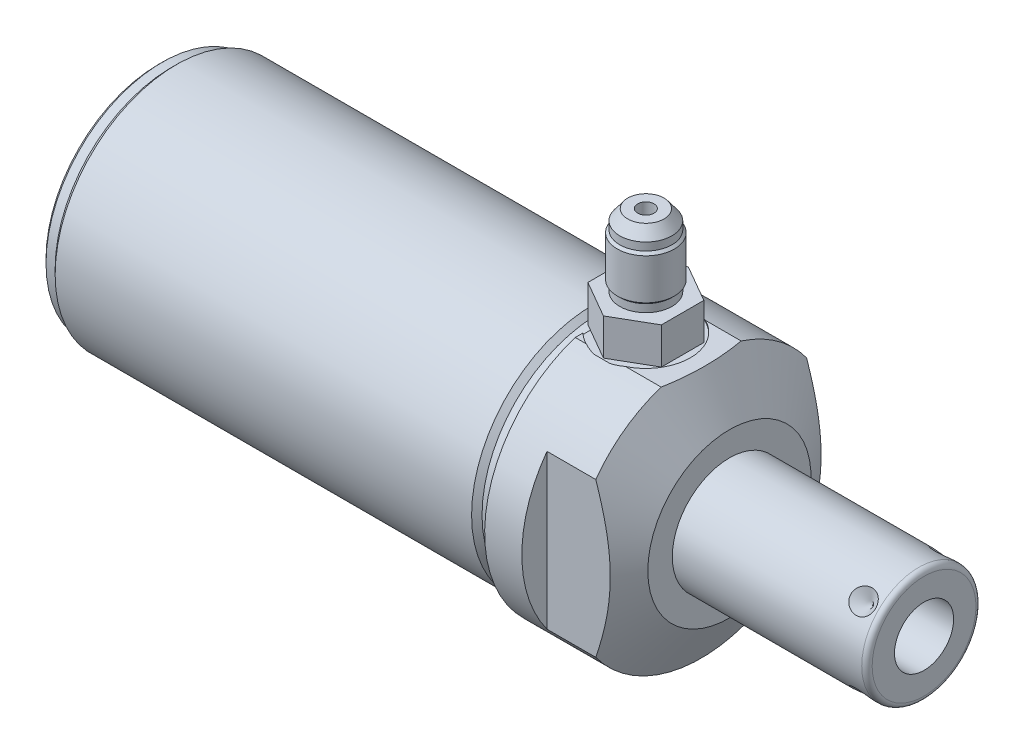
SolidWorks part; units mm, degrees
material "Alloy Steel"
ref_plane "Front Plane" through (0, 0, 0) normal (0, 0, 1) x (1, 0, 0)
ref_plane "Top Plane" through (0, 0, 0) normal (0, 1, 0) x (1, 0, 0)
ref_plane "Right Plane" through (0, 0, 0) normal (1, 0, 0) x (0, 0, -1)
ref_plane "Plane1" through (0, 0, 0) normal (1, 0, 0) x (0, 0, -1)
sketch "Sketch1" plane through (0, 0, 0) normal (1, 0, 0) x (0, 0, -1)
  circle A0 centre (0, 0) radius 25.4
  dimension "D1" = 50.8
extrude "Extrude1" add sketch "Sketch1" along normal blind 22.225 and the other way blind 88.9
ref_plane "Plane2" through (0, 0, 0) normal (1, 0, 0) x (0, 0, -1)
sketch "Sketch2" plane through (0, 0, 0) normal (1, 0, 0) x (0, 0, -1)
  line L0 (-25.9842, 0) -> (25.9842, 0) construction
  circle A0 centre (0, 0) radius 23.622
  circle A1 centre (0, 0) radius 25.4 construction
  circle A2 centre (0, 0) radius 25.4
  dimension "D1" = 47.244
extrude "Cut-Extrude1" cut sketch "Sketch2" against normal up to next
ref_plane "Plane4" through (0, 0, 0) normal (-1, 0, 0) x (0, 0, 1)
sketch "Sketch4" plane through (0, 0, 0) normal (-1, 0, 0) x (0, 0, 1)
  line L0 (20.5105, -14.9826) -> (20.5105, 14.9826)
  line L1 (7.7749, 24.1808) -> (-7.7749, 24.1808)
  line L2 (-20.5105, -14.9826) -> (-20.5105, 14.9826)
  line L4 (0, -27.879) -> (0, 26.6598) construction
  circle A0 centre (0, 0) radius 25.4 construction
  arc A2 (7.7749, 24.1808) -> (-7.7749, 24.1808) centre (0, 0) ccw
  arc A3 (20.5105, -14.9826) -> (20.5105, 14.9826) centre (0, 0) ccw
  arc A4 (-20.5105, 14.9826) -> (-20.5105, -14.9826) centre (0, 0) ccw
  dimension "D1" = 41.021
  dimension "D2" = 24.1808
extrude "Cut-Extrude3" cut sketch "Sketch4" against normal up to next from offset 7.239
ref_plane "Plane6" through (0, 0, 0) normal (0, 0, 1) x (1, 0, 0)
sketch "Sketch19" plane through (7.239, 0, 0) normal (1, 0, 0) x (0, 0, -1)
  line L1 (-7.7749, 24.1808) -> (7.7749, 24.1808)
  line L2 (-7.7749, 24.1808) -> (7.7749, 24.1808)
  arc A1 (7.7749, 24.1808) -> (-7.7749, 24.1808) centre (0, 0) ccw
  arc A2 (7.7749, 24.1808) -> (-7.7749, 24.1808) centre (0, 0) ccw
  dimension "D1" = 0
extrude "Cut-Extrude4" cut sketch "Sketch19" against normal up to surface (7.239 mm away) up to face at (0, 0, -23.622)
sketch "Sketch6" plane through (0, 0, 0) normal (0, 0, 1) x (1, 0, 0)
  line L0 (2.061, 50.8) -> (22.225, 15.875)
  line L1 (1.0528, 0) -> (23.2332, 0) construction
  line L2 (22.225, 14.9826) -> (22.225, 24.1808) construction
  line L3 (22.225, 15.875) -> (22.225, 50.8)
  line L4 (22.225, 50.8) -> (2.061, 50.8)
  line L5 (22.225, 14.9826) -> (22.225, -14.9826) construction
  dimension "D1" = 15.875
  dimension "D2" = 30
  dimension "D3" = 50.8
revolve "Cut-Revolve2" cut sketch "Sketch6" angle 360 about L1
ref_plane "Plane7" through (5.969, 23.9268, 0) normal (0, 0, 1) x (1, 0, 0)
sketch "S2D0002" plane through (5.969, 23.9268, 0) normal (0, 0, 1) x (1, 0, 0)
  line L0 (0, 0) -> (4.5466, 0)
  line L1 (4.5466, 0) -> (4.1066, -2.0701)
  line L2 (4.1066, -2.0701) -> (3.4544, -2.7223)
  line L3 (3.4544, -2.7223) -> (3.4544, -12.192)
  line L4 (3.4544, -12.192) -> (0, -12.192)
  line L5 (0, -12.192) -> (0, 0)
  line L6 (0, -12.8016) -> (0, 0.6096) construction
  dimension "D1" = 12.192
revolve "Cut-Revolve3" cut sketch "S2D0002" angle 360 about L6
sketch "Sketch20" plane through (0, 24.1808, 0) normal (0, 1, 0) x (1, 0, 0)
  circle A0 centre (5.969, 0) radius 8.6614
  dimension "D1" = 17.3228
extrude "Cut-Extrude5" cut sketch "Sketch20" against normal blind 0.254
ref_plane "Plane9" through (0, 0, 0) normal (0, 0, 1) x (1, 0, 0)
sketch "Sketch9" plane through (0, 0, 0) normal (0, 0, 1) x (1, 0, 0)
  line L0 (0, 23.622) -> (0, 22.606)
  line L1 (0, 22.606) -> (-3.302, 22.606)
  line L2 (-3.302, 22.606) -> (-4.318, 23.622)
  line L3 (-4.5339, 0) -> (0.2159, 0) construction
  line L4 (0, 23.622) -> (-4.318, 23.622)
  line L5 (0, 23.622) -> (-88.9, 23.622) construction
  line L6 (0, 23.622) -> (0, -23.622) construction
  dimension "D1" = 45.212
  dimension "D2" = 3.302
  dimension "D3" = 45
revolve "Cut-Revolve5" cut sketch "Sketch9" angle 360 about L3
ref_plane "Plane11" through (0, 0, 0) normal (0, 0, 1) x (1, 0, 0)
sketch "Sketch11" plane through (0, 0, 0) normal (0, 0, 1) x (1, 0, 0)
  line L0 (-88.9, 23.622) -> (-88.9, 22.606)
  line L1 (-88.9, 22.606) -> (-86.36, 22.606)
  line L2 (-86.36, 22.606) -> (-85.344, 23.622)
  line L3 (-89.0778, 0) -> (-85.1662, 0) construction
  line L4 (-88.9, 23.622) -> (-85.344, 23.622)
  line L5 (-4.318, 23.622) -> (-88.9, 23.622) construction
  line L6 (-88.9, 23.622) -> (-88.9, -23.622) construction
  dimension "D1" = 45.212
  dimension "D2" = 2.54
  dimension "D3" = 45
revolve "Cut-Revolve7" cut sketch "Sketch11" angle 360 about L3
chamfer "Chamfer1" distance 0.762 angle 45 1 edges at (-88.9, 0, 22.606)
ref_plane "Plane12" through (0, 0, 0) normal (0, 0, 1) x (0, -1, 0)
sketch "Sketch12" plane through (0, 0, 0) normal (0, 0, 1) x (0, -1, 0)
  line L0 (0, 22.225) -> (0, 60.0964)
  line L1 (0, 60.0964) -> (10.0965, 60.0964)
  line L2 (11.1125, 59.0804) -> (11.1125, 22.225)
  line L3 (11.1125, 22.225) -> (0, 22.225)
  line L4 (0, 20.3314) -> (0, 61.99) construction
  line L5 (15.875, 22.225) -> (-15.875, 22.225) construction
  line L6 (-24.1808, 0) -> (25.4, 0) construction
  arc A0 (11.1125, 59.0804) -> (10.0965, 60.0964) centre (10.0965, 59.0804) ccw
  dimension "D3" = 1.016
  dimension "D1" = 22.225
  dimension "D2" = 60.0964
revolve "Revolve1" add sketch "Sketch12" angle 360 about L4
ref_plane "Plane13" through (60.0964, -5.7531, 0) normal (0, 0, 1) x (0, -1, 0)
sketch "S2D0001" plane through (60.0964, -5.7531, 0) normal (0, 0, 1) x (0, -1, 0)
  line L0 (0, 0) -> (0, -17.018)
  line L1 (0, -17.018) -> (-5.7531, -20.4748)
  line L2 (0, 0) -> (-5.7531, 0)
  line L3 (-5.7531, 0) -> (-5.7531, -20.4748)
  line L4 (-5.7531, -21.4986) -> (-5.7531, 1.0237) construction
  line L6 (4.3434, 0) -> (-15.8496, 0) construction
  dimension "D1" = 11.5062
  dimension "D2" = 59
  dimension "D3" = 17.018
revolve "Cut-Revolve8" cut sketch "S2D0001" angle 360 about L4
ref_plane "Plane15" through (7.239, 0, 0) normal (1, 0, 0) x (0, 0, 1)
ref_plane "Plane16" through (0, 23.9268, 0) normal (0, 1, 0) x (0, 0, 1)
sketch "S2D0003" plane through (0, 23.9268, 0) normal (0, 1, 0) x (0, 0, 1)
  line L0 (-4.1281, 13.1191) -> (4.1281, 13.1191)
  line L1 (4.1281, 13.1191) -> (8.2562, 5.969)
  line L2 (8.2562, 5.969) -> (4.1281, -1.1811)
  line L3 (4.1281, -1.1811) -> (-4.1281, -1.1811)
  line L4 (-4.1281, -1.1811) -> (-8.2562, 5.969)
  line L5 (-8.2562, 5.969) -> (-4.1281, 13.1191)
  line L6 (-9.0818, 5.969) -> (9.0818, 5.969) construction
  dimension "D1" = 14.3002
ref_plane "Plane17" through (0, 31.0388, 0) normal (0, 1, 0) x (0, 0, 1)
extrude "Extrude3" add sketch "S2D0003" against normal up to surface
ref_plane "Plane18" through (0, 0, 0) normal (0, 0, 1) x (0, -1, 0)
sketch "Sketch16" plane through (0, 0, 0) normal (0, 0, 1) x (0, -1, 0)
  line L0 (-31.0388, 11.049) -> (-32.5628, 11.049)
  line L1 (-32.5628, 11.049) -> (-33.0327, 11.5189)
  line L2 (-33.0327, 11.5189) -> (-40.9575, 11.5189)
  line L3 (-40.9575, 11.5189) -> (-41.4274, 11.049)
  line L4 (-41.4274, 11.049) -> (-42.9514, 11.049)
  line L5 (-42.9514, 11.049) -> (-45.0088, 9.4986)
  line L6 (-45.0088, 9.4986) -> (-45.0088, 7.5565)
  line L7 (-45.0088, 7.5565) -> (-31.0388, 7.5565)
  line L8 (-31.0388, 7.5565) -> (-31.0388, 11.049)
  line L9 (-45.7073, 5.969) -> (-30.3403, 5.969) construction
  line L10 (-22.606, 0) -> (22.606, 0) construction
  line L11 (-31.0388, 5.969) -> (-31.0388, 13.1191) construction
  dimension "D1" = 5.969
  dimension "D2" = 3.175
  dimension "D3" = 13.97
  dimension "D4" = 37
  dimension "D5" = 10.16
  dimension "D6" = 7.0593
  dimension "D7" = 11.0998
  dimension "D8" = 45
  dimension "D9" = 1.524
  dimension "D10" = 10.16
  dimension "D11" = 45
  dimension "D12" = 4.0513
revolve "Revolve2" add sketch "Sketch16" angle 360 about L9
ref_plane "Plane19" through (56.134, -11.1125, 0) normal (0, 0, 1) x (-1, 0, 0)
ref_plane "Plane20" through (0, 0, 0) normal (0, 0.7071, 0.7071) x (-1, 0, 0)
sketch "Sketch17" plane through (56.134, 7.8577, -7.8577) normal (0, -0.7071, -0.7071) x (-1, 0, 0)
  line L0 (0, 0) -> (2.413, 0)
  line L1 (2.413, 0) -> (0, -2.413)
  line L2 (0, 0) -> (0, -2.413)
  line L3 (0, -2.5337) -> (0, 0.1207) construction
  line L4 (33.909, 0) -> (-2.9464, 0) construction
  line L5 (-3.9624, -1.016) -> (-3.9624, -21.209) construction
  dimension "D1" = 3.9624
  dimension "D2" = 4.826
  dimension "D3" = 45
revolve "Cut-Revolve9" cut sketch "Sketch17" angle 360 about L3
pattern_circular "CirPattern1" count 4 over 360 about axis through (-88.901, 0, 0) along (1, 0, 0) of "Cut-Revolve9"
